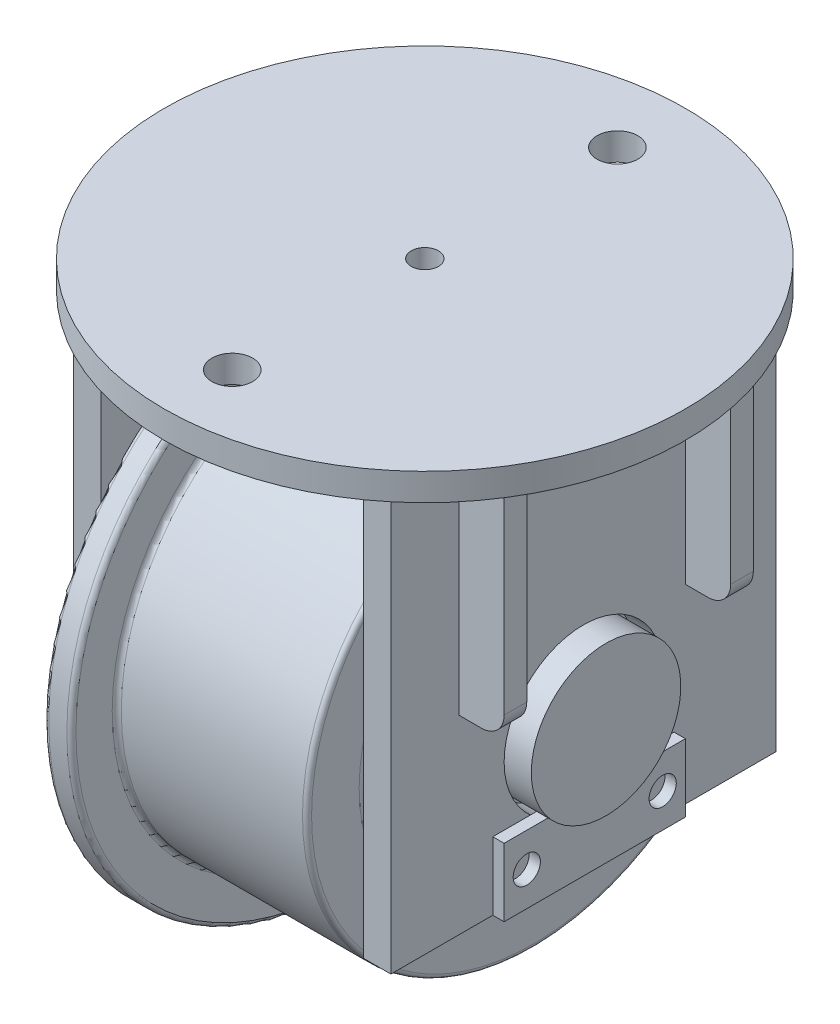
SolidWorks part; units mm, degrees
ref_plane "Front Plane" through (0, 0, 0) normal (0, 0, 1) x (1, 0, 0)
ref_plane "Top Plane" through (0, 0, 0) normal (0, 1, 0) x (1, 0, 0)
ref_plane "Right Plane" through (0, 0, 0) normal (1, 0, 0) x (0, 0, -1)
sketch "Sketch1" plane through (0, 0, 0) normal (0, 1, 0) x (1, 0, 0)
  line L0 (0, 115) -> (0, -115) construction
  line L1 (-115, 0) -> (115, 0) construction
  circle A0 centre (0, 0) radius 115
  circle A1 centre (0, 0) radius 85 construction
  circle A2 centre (0, 85) radius 9
  circle A3 centre (-85, 0) radius 9 construction
  circle A4 centre (0, -85) radius 9
  circle A5 centre (85, 0) radius 9 construction
  circle A6 centre (0, 0) radius 6
  dimension "D1" = 230
  dimension "D2" = 18
  dimension "D3" = 170
  dimension "D4" = 12
extrude "Boss-Extrude1" add sketch "Sketch1" along normal mid plane 12
sketch "Sketch2" plane through (0, -6, 0) normal (0, -1, 0) x (-1, 0, 0)
  line L1 (70, -85) -> (58, -85)
  line L2 (70, -85) -> (70, 85)
  line L3 (70, 85) -> (58, 85)
  line L4 (58, -85) -> (58, 85)
  line L5 (70, -85) -> (58, 85) construction
  line L6 (70, 85) -> (58, -85) construction
  point P0 (64, 0)
  dimension "D1" = 12
  dimension "D2" = 170
  dimension "D3" = 58
extrude "Boss-Extrude2" add sketch "Sketch2" along normal blind 184
sketch "Sketch3" plane through (-70, 0, 0) normal (-1, 0, 0) x (0, 0, 1)
  line L0 (0, 0) -> (0, -156.5188) construction
  line L1 (115, 6) -> (-115, 6) construction
  circle A0 centre (0, -134) radius 35
  dimension "D2" = 70
  dimension "D1" = 140
extrude "Cut-Extrude1" cut sketch "Sketch3" against normal blind 184
sketch "Sketch6" plane through (-70, 0, 0) normal (-1, 0, 0) x (0, 0, 1)
  line L0 (-50, -6) -> (-50, -106)
  line L1 (85, -6) -> (-85, -6) construction
  line L2 (50, -6) -> (50, -106)
  dimension "D1" = 100
  dimension "D2" = 50
  dimension "D3" = 50
extrude "Extrude-Thin1" add sketch "Sketch6" along normal blind 20 thin thin type mid plane wall 10
fillet "Fillet2" radius 10 2 edges at (-90, -106, 50) (-90, -106, -50)
mirror "Mirror1" about plane through (0, 0, 0) normal (1, 0, 0) of "Fillet2", "Cut-Extrude1", "Boss-Extrude2", "Extrude-Thin1"
sketch "Sketch4" plane through (0, 0, 0) normal (0, 0, 1) x (1, 0, 0)
  line L0 (-70, -134) -> (70, -134) construction
  line L1 (-70, -99) -> (-70, -169) construction
  line L2 (70, -169) -> (70, -99) construction
sketch "Sketch5" plane through (0, 0, 0) normal (0, 0, 1) x (1, 0, 0)
  line L0 (-53, -99) -> (-53, -59)
  line L1 (-53, -59) -> (-48, -59)
  line L2 (-48, -59) -> (-48, -14)
  line L3 (-48, -14) -> (-36, -14)
  line L4 (-36, -14) -> (-36, -34)
  line L5 (-36, -34) -> (48, -34)
  line L6 (48, -34) -> (48, -59)
  line L7 (48, -59) -> (53, -59)
  line L8 (53, -59) -> (53, -99)
  line L9 (53, -99) -> (-53, -99)
  line L10 (-70, -134) -> (70, -134) construction
  line L11 (-58, -190) -> (-58, -6) construction
  line L12 (58, -190) -> (58, -6) construction
  line L14 (-78, -101) -> (80, -101)
  line L15 (-78, -101) -> (-78, -134)
  line L16 (-78, -134) -> (80, -134)
  line L17 (80, -101) -> (80, -134)
  line L18 (-70, -190) -> (-70, -6) construction
  line L19 (70, -190) -> (70, -6) construction
  dimension "D1" = 120
  dimension "D2" = 100
  dimension "D3" = 35
  dimension "D4" = 5
  dimension "D5" = 5
  dimension "D6" = 40
  dimension "D7" = 5
  dimension "D8" = 12
  dimension "D9" = 2
  dimension "D10" = 8
  dimension "D11" = 10
revolve "Revolve1" add sketch "Sketch5" angle 360 about L0
fillet "Fillet1" radius 2 8 edges at (53, -134, 75) (48, -134, 75) (48, -134, 100) (-36, -134, 100) (-36, -134, 120) (-48, -134, 120) (-48, -134, 75) (-53, -134, 75)
sketch "Sketch7" plane through (70, 0, 0) normal (1, 0, 0) x (0, 0, -1)
  line L0 (0, -134) -> (0, -175) construction
  line L1 (40, -160) -> (-40, -160)
  line L2 (40, -160) -> (40, -190)
  line L3 (40, -190) -> (-40, -190)
  line L4 (-40, -160) -> (-40, -190)
  line L5 (40, -160) -> (-40, -190) construction
  line L6 (40, -190) -> (-40, -160) construction
  line L7 (-85, -190) -> (85, -190) construction
  line L8 (-40, -175) -> (40, -175) construction
  circle A0 centre (-30, -175) radius 6
  circle A1 centre (30, -175) radius 6
  point P0 (0, -175)
  point P16 (-29.8856, -175)
  point P17 (30.4571, -175)
  dimension "D3" = 12
  dimension "D5" = 10
  dimension "D1" = 80
  dimension "D2" = 30
  dimension "D4" = 10
extrude "Boss-Extrude3" add sketch "Sketch7" along normal blind 5 separate body
